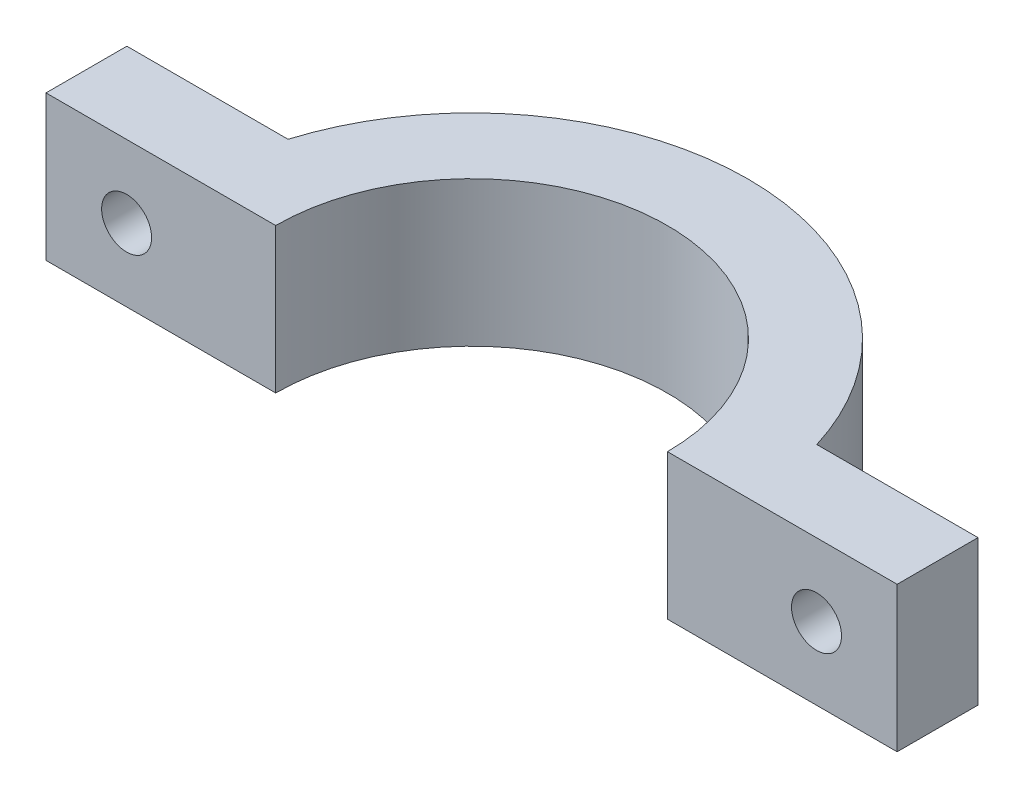
SolidWorks part; units mm, degrees
ref_plane "Front Plane" through (0, 0, 0) normal (0, 0, 1) x (1, 0, 0)
ref_plane "Top Plane" through (0, 0, 0) normal (0, 1, 0) x (1, 0, 0)
ref_plane "Right Plane" through (0, 0, 0) normal (1, 0, 0) x (0, 0, -1)
sketch "Sketch1" plane through (0, 0, 0) normal (0, 1, 0) x (1, 0, 0)
  line L2 (16.4, 5.0162) -> (26.4, 5.0162)
  line L3 (12.15, 0) -> (26.4, 0)
  line L5 (26.4, 5.0162) -> (26.4, 0)
  line L6 (0, -8.3817) -> (0, 8.3817) construction
  line L7 (-12.15, 0) -> (-26.4, 0)
  line L8 (-26.4, 5.0162) -> (-26.4, 0)
  line L9 (-16.4, 5.0162) -> (-26.4, 5.0162)
  arc A0 (12.15, 0) -> (-12.15, 0) centre (0, 0) ccw
  arc A1 (16.4, 5.0162) -> (-16.4, 5.0162) centre (0, 0) ccw
  point P6 (0, 0)
  point P11 (0, 5)
  point P12 (0, 0)
  dimension "D1" = 24.3
  dimension "D2" = 5
  dimension "D3" = 10
  dimension "D4" = 52.8
  dimension "D5" = 10
  dimension "D6" = 14.25
extrude "Boss-Extrude1" add sketch "Sketch1" along normal blind 9
sketch "Sketch2" plane through (0, 0, -5.0162) normal (0, 0, -1) x (-1, 0, 0)
  line L4 (-26.4, 0) -> (-16.4, 0)
  line L5 (-16.4, 0) -> (-16.4, 9)
  line L6 (-16.4, 9) -> (-26.4, 9)
  line L7 (-26.4, 9) -> (-26.4, 0)
  line L8 (-26.4, 0) -> (-16.4, 0)
  line L9 (-16.4, 0) -> (-16.4, 9)
  line L10 (-16.4, 9) -> (-26.4, 9)
  line L11 (-26.4, 9) -> (-26.4, 0)
  circle A0 centre (-21.4, 4.5) radius 1.55
  dimension "D2" = 3.1
  dimension "D3" = 5
  dimension "D1" = 0
extrude "Cut-Extrude1" cut sketch "Sketch2" against normal blind 9 contours A0
mirror "Mirror1" about plane through (0, 0, 0) normal (1, 0, 0) of "Cut-Extrude1"
